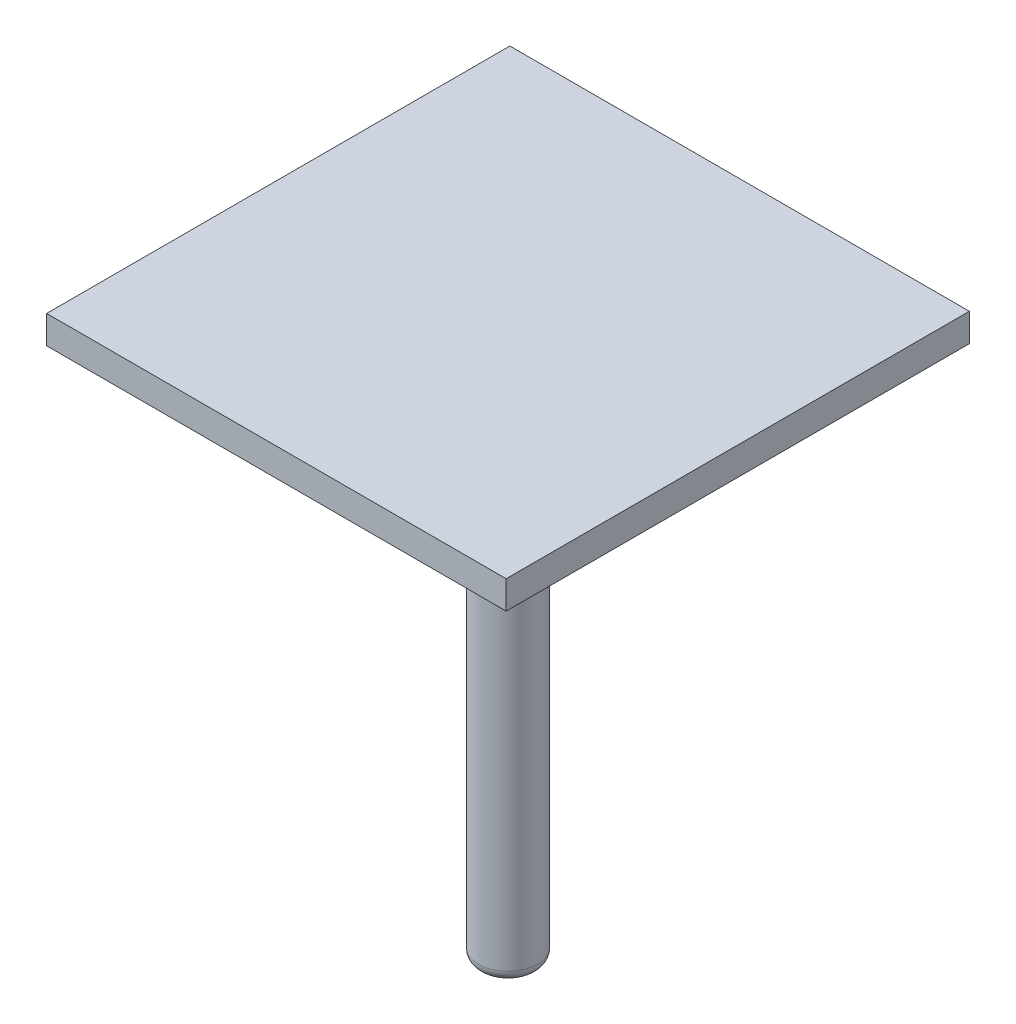
SolidWorks part; units mm, degrees
ref_plane "Front Plane" through (0, 0, 0) normal (0, 0, 1) x (1, 0, 0)
ref_plane "Top Plane" through (0, 0, 0) normal (0, 1, 0) x (1, 0, 0)
ref_plane "Right Plane" through (0, 0, 0) normal (1, 0, 0) x (0, 0, -1)
sketch "Sketch1" plane through (0, 0, 0) normal (0, 1, 0) x (1, 0, 0)
  circle A0 centre (0, 0) radius 1.05
  dimension "D1" = 2.1
extrude "Boss-Extrude1" add sketch "Sketch1" along normal blind 16.5
sketch "Sketch2" plane through (0, 16.5, 0) normal (0, 1, 0) x (1, 0, 0)
  circle A0 centre (0, 0) radius 2
  dimension "D1" = 4
extrude "Boss-Extrude2" add sketch "Sketch2" along normal blind 2.5
fillet "Fillet1" radius 0.4 1 edges at (0, 0, 1.05)
fillet "Fillet2" radius 1 1 edges at (0, 19, 2)
sketch "Sketch3" plane through (0, 19, 0) normal (0, 1, 0) x (1, 0, 0)
  line L1 (-8.1898, -8.2559) -> (8.1898, -8.2559)
  line L2 (-8.1898, -8.2559) -> (-8.1898, 8.2559)
  line L3 (-8.1898, 8.2559) -> (8.1898, 8.2559)
  line L4 (8.1898, -8.2559) -> (8.1898, 8.2559)
  line L5 (-8.1898, -8.2559) -> (8.1898, 8.2559) construction
  line L6 (-8.1898, 8.2559) -> (8.1898, -8.2559) construction
  point P0 (0, 0)
extrude "Boss-Extrude3" add sketch "Sketch3" along normal blind 1
